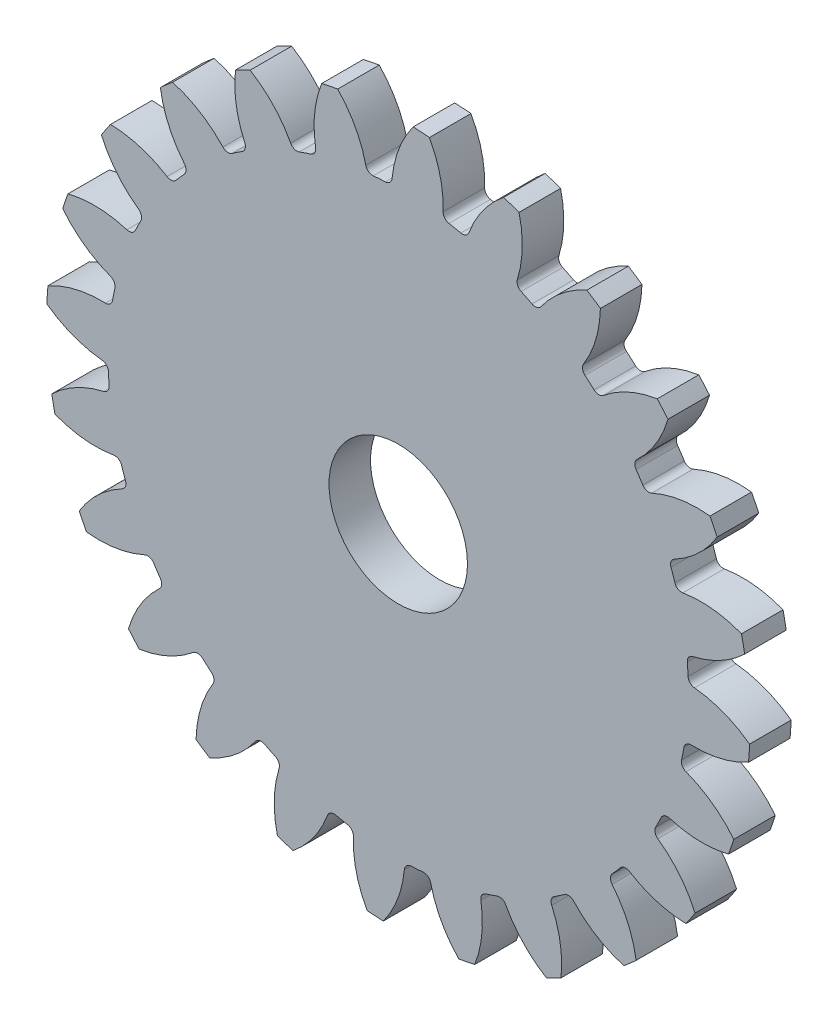
SolidWorks part; units mm, degrees
ref_plane "Alzado" through (0, 0, 0) normal (0, 0, 1) x (1, 0, 0)
ref_plane "Planta" through (0, 0, 0) normal (0, 1, 0) x (1, 0, 0)
ref_plane "Vista lateral" through (0, 0, 0) normal (1, 0, 0) x (0, 0, -1)
sketch "Croquis1" plane through (0, 0, 0) normal (0, 0, 1) x (1, 0, 0)
  circle A0 centre (0, 0) radius 25.4
  dimension "D1" = 50.8
extrude "Saliente-Extruir1" add sketch "Croquis1" along normal blind 3
sketch "Croquis2" plane through (0, 0, 3) normal (0, 0, 1) x (1, 0, 0)
  line L0 (0, 0) -> (0, 23.368) construction
  line L1 (0, 0) -> (9.0718, 24.9247) construction
  line L2 (0, 0) -> (-1.524, 23.3183) construction
  line L3 (0, 23.368) -> (7.5103, 20.6345) construction
  arc A0 (1.0773, 25.3771) -> (-4.3711, 25.0211) centre (0, 0) ccw
  arc A2 (-0.4758, 20.9496) -> (-2.255, 20.8333) centre (0, 0) ccw
  arc A3 (1.0773, 25.3771) -> (-0.4758, 20.9496) centre (7.5103, 20.6345) ccw
  arc A4 (-4.3711, 25.0211) -> (-2.255, 20.8333) centre (-10.1322, 19.4814) cw
  dimension "D2" = 41.91
  dimension "D3" = 20
  dimension "D4" = 1.524
extrude "Cortar-Extruir1" cut sketch "Croquis2" against normal through all
fillet "Redondeo1" radius 0.508 2 edges at (-0.4758, 20.9496, 1.5) (-2.255, 20.8333, 1.5)
pattern_circular "MatrizC1" count 24 over 360 about axis through (0, 0, 0) along (0, 0, 1) of "Redondeo1", "Cortar-Extruir1"
sketch "Croquis3" plane through (0, 0, 3) normal (0, 0, 1) x (1, 0, 0)
  circle A0 centre (0, 0) radius 5
  dimension "D1" = 10
extrude "Cortar-Extruir2" cut sketch "Croquis3" against normal through all
